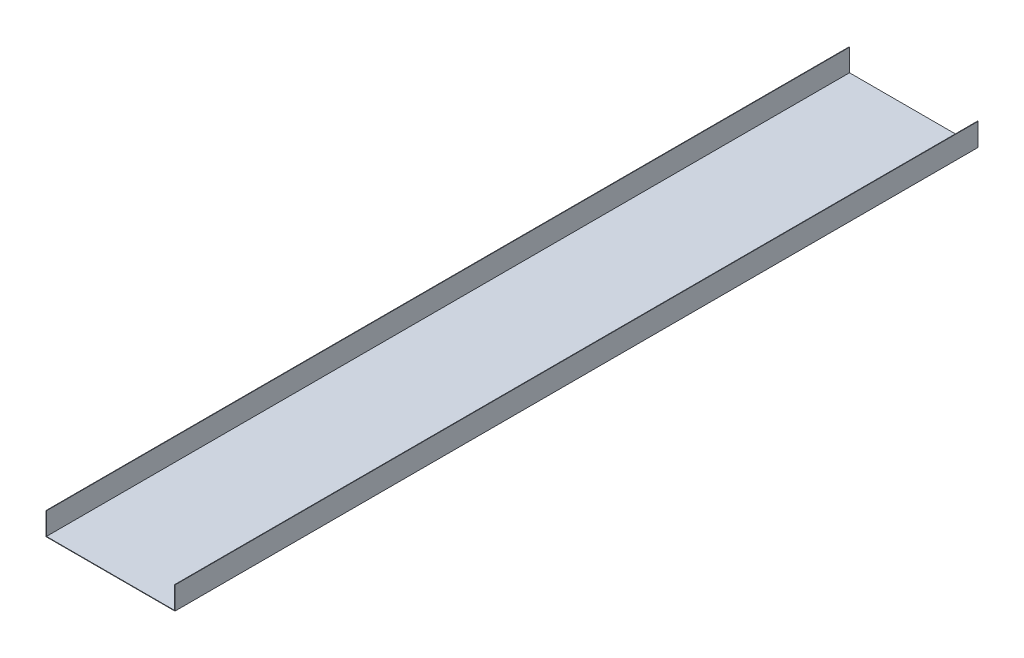
SolidWorks part; units mm, degrees
ref_plane "前基準面" through (0, 0, 0) normal (0, 0, 1) x (1, 0, 0)
ref_plane "上基準面" through (0, 0, 0) normal (0, 1, 0) x (1, 0, 0)
ref_plane "右基準面" through (0, 0, 0) normal (1, 0, 0) x (0, 0, -1)
sketch "草圖1" plane through (0, 0, 0) normal (0, 1, 0) x (1, 0, 0)
  line L1 (-6775, 42500) -> (6775, 42500)
  line L2 (-6775, 42500) -> (-6775, -42500)
  line L3 (-6775, -42500) -> (6775, -42500)
  line L4 (6775, 42500) -> (6775, -42500)
  line L5 (-6775, 42500) -> (6775, -42500) construction
  line L6 (-6775, -42500) -> (6775, 42500) construction
  point P0 (0, 0)
  dimension "D1" = 85000
  dimension "D2" = 13550
extrude "填料-伸長1" add sketch "草圖1" against normal blind 50
sketch "草圖2" plane through (0, 0, 42500) normal (0, 0, 1) x (1, 0, 0)
  line L0 (0, -362.2223) -> (0, 4740.9061) construction
  line L1 (-6775, -50) -> (-6825, -50)
  line L2 (-6775, -50) -> (-6775, 2350)
  line L3 (-6775, 2350) -> (-6825, 2350)
  line L4 (-6825, -50) -> (-6825, 2350)
  line L5 (6825, -50) -> (6825, 2350)
  line L6 (6775, 2350) -> (6825, 2350)
  line L7 (6775, -50) -> (6775, 2350)
  line L8 (6775, -50) -> (6825, -50)
  dimension "D1" = 2400
  dimension "D2" = 50
extrude "填料-伸長2" add sketch "草圖2" against normal up to surface (85000 mm away) up to face at (0, -25, -42500)
